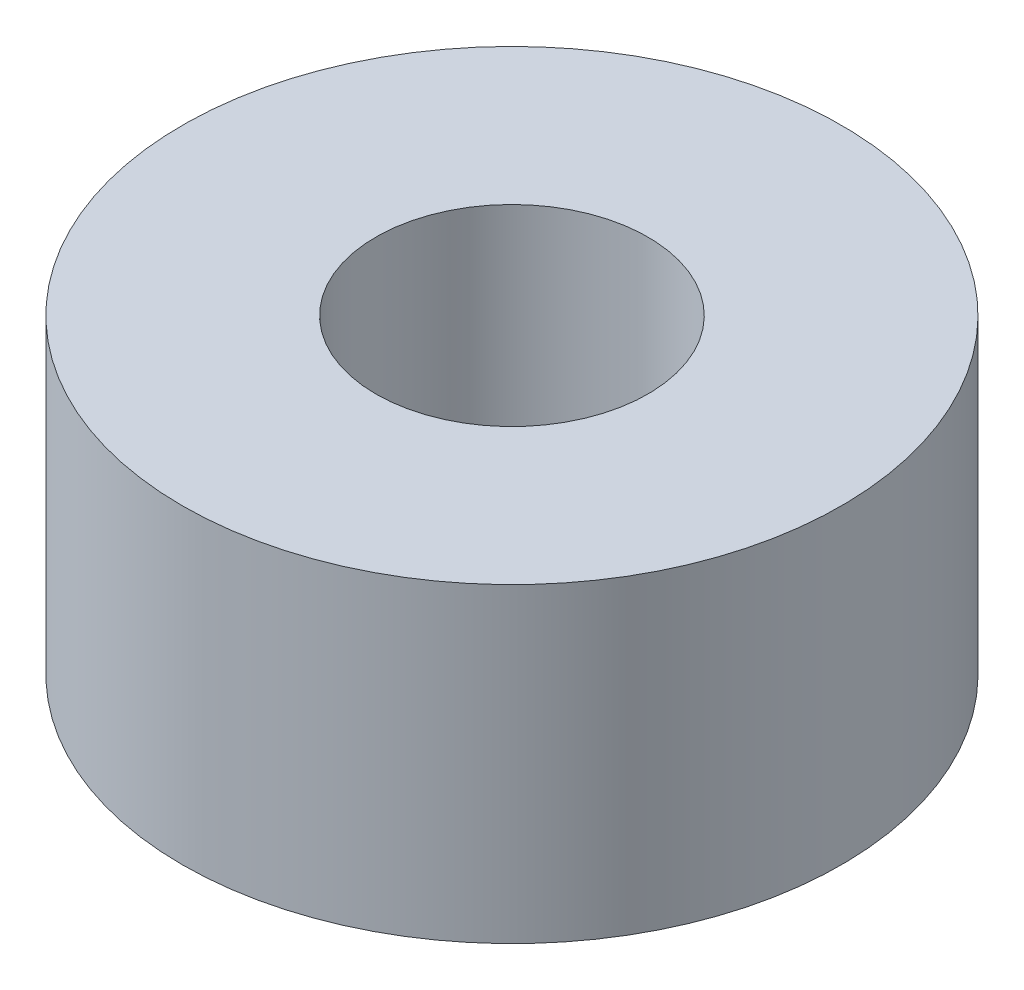
SolidWorks part; units mm, degrees
material "UHMW"
ref_plane "Front" through (0, 0, 0) normal (0, 0, 1) x (1, 0, 0)
ref_plane "Top" through (0, 0, 0) normal (0, 1, 0) x (1, 0, 0)
ref_plane "Right" through (0, 0, 0) normal (1, 0, 0) x (0, 0, -1)
sketch "Sketch1" plane through (0, 0, 0) normal (0, 1, 0) x (1, 0, 0)
  circle A0 centre (0, 0) radius 5.5562
  circle A1 centre (0, 0) radius 13.462
  dimension "D1" = 26.924
  dimension "D2" = 11.1125
extrude "Boss-Extrude1" add sketch "Sketch1" along normal blind 12.7
